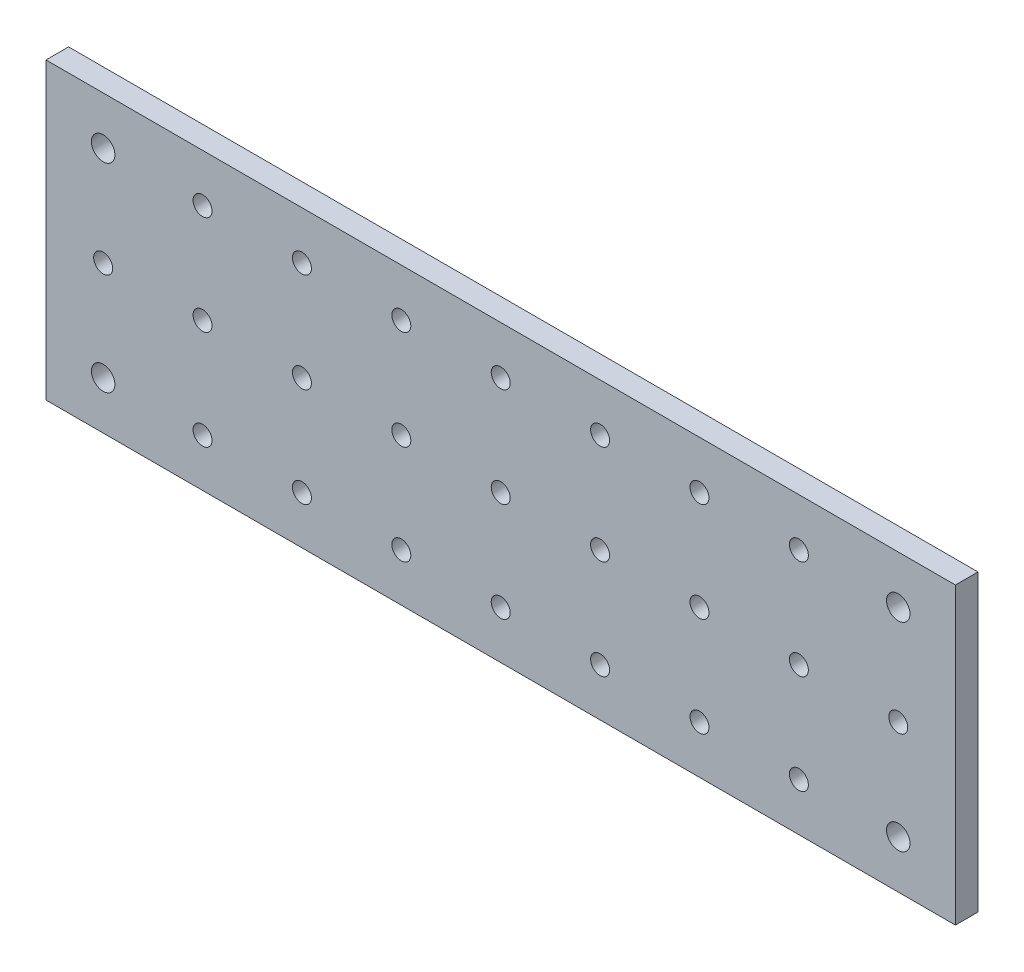
SolidWorks part; units mm, degrees
ref_plane "Plano frontal" through (0, 0, 0) normal (0, 0, 1) x (1, 0, 0)
ref_plane "Plano superior" through (0, 0, 0) normal (0, 1, 0) x (1, 0, 0)
ref_plane "Plano direito" through (0, 0, 0) normal (1, 0, 0) x (0, 0, -1)
sketch "Esboço1" plane through (0, 0, 0) normal (0, 0, 1) x (1, 0, 0)
  line L1 (0, 0) -> (201.3, 0)
  line L2 (0, 0) -> (0, 65.2)
  line L3 (0, 65.2) -> (201.3, 65.2)
  line L4 (201.3, 0) -> (201.3, 65.2)
  dimension "D1" = 201.3
  dimension "65.2" = 65.2
extrude "Ressalto-extrusão1" add sketch "Esboço1" along normal blind 5
sketch "Esboço2" plane through (0, 0, 0) normal (0, 0, 1) x (1, 0, 0)
  line L0 (0, 32.6) -> (201.3, 32.6) construction
  line L1 (0, 65.2) -> (0, 0) construction
  line L2 (201.3, 0) -> (201.3, 65.2) construction
  line L3 (201.3, 32.6) -> (100.65, 65.2) construction
  line L4 (201.3, 65.2) -> (0, 65.2) construction
  line L5 (100.65, 65.2) -> (100.65, 0) construction
  line L6 (0, 0) -> (201.3, 0) construction
  line L7 (100.65, 87.2) -> (100.65, 22) construction
  line L8 (100.65, 32.6) -> (100.65, 54.6) construction
  line L9 (100.65, 43.2) -> (100.65, -22) construction
  line L10 (100.65, 32.6) -> (100.65, 10.6) construction
  line L11 (122.65, 32.6) -> (122.65, 54.6) construction
  line L12 (122.65, 32.6) -> (122.65, 10.6) construction
  line L13 (144.65, 32.6) -> (144.65, 54.6) construction
  line L14 (144.65, 32.6) -> (144.65, 10.6) construction
  line L15 (166.65, 32.6) -> (166.65, 54.6) construction
  line L16 (166.65, 32.6) -> (166.65, 10.6) construction
  line L17 (188.65, 32.6) -> (188.65, 54.6) construction
  line L18 (188.65, 32.6) -> (188.65, 10.6) construction
  line L19 (100.65, 32.6) -> (122.65, 32.6) construction
  line L20 (78.65, 32.6) -> (78.65, 54.6) construction
  line L21 (78.65, 32.6) -> (78.65, 10.6) construction
  line L22 (56.65, 32.6) -> (56.65, 54.6) construction
  line L23 (56.65, 32.6) -> (56.65, 10.6) construction
  line L24 (34.65, 32.6) -> (34.65, 54.6) construction
  line L25 (34.65, 32.6) -> (34.65, 10.6) construction
  line L26 (12.65, 32.6) -> (12.65, 54.6) construction
  line L27 (12.65, 32.6) -> (12.65, 10.6) construction
  line L28 (100.65, 32.6) -> (78.65, 32.6) construction
  circle A0 centre (100.65, 32.6) radius 2.1
  circle A1 centre (100.65, 54.6) radius 2.1
  circle A2 centre (100.65, 10.6) radius 2.1
  circle A3 centre (122.65, 32.6) radius 2.1
  circle A4 centre (122.65, 54.6) radius 2.1
  circle A5 centre (122.65, 10.6) radius 2.1
  circle A6 centre (144.65, 32.6) radius 2.1
  circle A7 centre (144.65, 54.6) radius 2.1
  circle A8 centre (144.65, 10.6) radius 2.1
  circle A9 centre (166.65, 32.6) radius 2.1
  circle A10 centre (166.65, 54.6) radius 2.1
  circle A11 centre (166.65, 10.6) radius 2.1
  circle A12 centre (188.65, 32.6) radius 2.1
  circle A13 centre (188.65, 54.6) radius 2.1
  circle A14 centre (188.65, 10.6) radius 2.1
  circle A15 centre (78.65, 32.6) radius 2.1
  circle A16 centre (78.65, 54.6) radius 2.1
  circle A17 centre (78.65, 10.6) radius 2.1
  circle A18 centre (56.65, 32.6) radius 2.1
  circle A19 centre (56.65, 54.6) radius 2.1
  circle A20 centre (56.65, 10.6) radius 2.1
  circle A21 centre (34.65, 32.6) radius 2.1
  circle A22 centre (34.65, 54.6) radius 2.1
  circle A23 centre (34.65, 10.6) radius 2.1
  circle A24 centre (12.65, 32.6) radius 2.1
  circle A25 centre (12.65, 54.6) radius 2.1
  circle A26 centre (12.65, 10.6) radius 2.1
  dimension "D1" = 4.2
  dimension "D2" = 22
  dimension "D3" = 22
  dimension "D6" = 22
  dimension "D7" = 22
  dimension "D5" = 2
  dimension "D4" = 2
extrude "Corte-extrusão1" cut sketch "Esboço2" along direction (0, 0, -1) on the side of the normal blind 30
sketch "Esboço3" plane through (0, 0, 0) normal (0, 0, -1) x (-1, 0, 0)
  line L0 (-190.75, 54.6) -> (-10.55, 54.6) construction
  line L1 (-10.55, 54.6) -> (-12.65, 56.7) construction
  line L2 (-12.65, 56.7) -> (-12.65, 8.5) construction
  line L3 (-12.65, 8.5) -> (-10.55, 10.6) construction
  line L4 (-10.55, 10.6) -> (-190.75, 10.6) construction
  line L5 (-190.75, 10.6) -> (-188.65, 8.5) construction
  line L6 (-188.65, 8.5) -> (-188.65, 56.7) construction
  circle A0 centre (-188.65, 54.6) radius 2.1 construction
  circle A1 centre (-12.65, 54.6) radius 2.1 construction
  circle A2 centre (-12.65, 10.6) radius 2.1 construction
  circle A3 centre (-188.65, 10.6) radius 2.1 construction
  circle A4 centre (-188.65, 54.6) radius 2.6
  circle A5 centre (-12.65, 54.6) radius 2.6
  circle A6 centre (-12.65, 10.6) radius 2.6
  circle A7 centre (-188.65, 10.6) radius 2.6
  dimension "D1" = 5.2
  dimension "D2" = 5.2
  dimension "D3" = 5.2
  dimension "D4" = 5.2
extrude "Corte-extrusão2" cut sketch "Esboço3" against normal blind 22 and the other way blind 28
